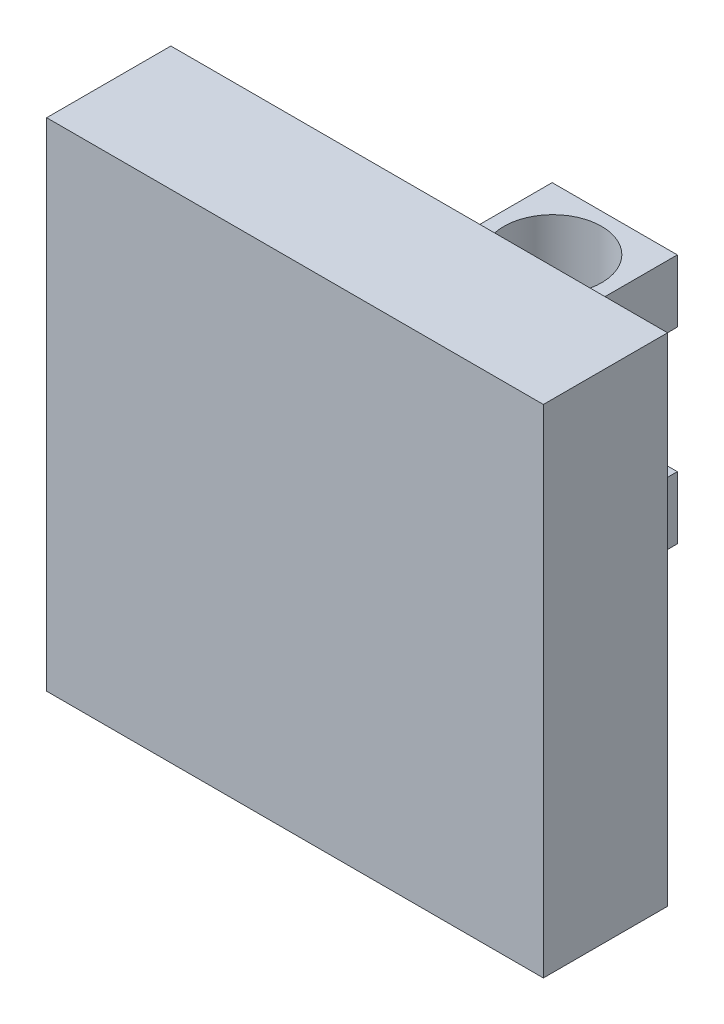
SolidWorks part; units mm, degrees
material "Acrylic (Medium-high impact)"
ref_plane "Front Plane" through (0, 0, 0) normal (0, 0, 1) x (1, 0, 0)
ref_plane "Top Plane" through (0, 0, 0) normal (0, 1, 0) x (1, 0, 0)
ref_plane "Right Plane" through (0, 0, 0) normal (1, 0, 0) x (0, 0, -1)
sketch "Sketch1" plane through (0, 0, 0) normal (0, 0, 1) x (1, 0, 0)
  line L1 (-12.7, -12.7) -> (12.7, -12.7)
  line L2 (-12.7, -12.7) -> (-12.7, 12.7)
  line L3 (-12.7, 12.7) -> (12.7, 12.7)
  line L4 (12.7, -12.7) -> (12.7, 12.7)
  line L5 (-12.7, -12.7) -> (12.7, 12.7) construction
  line L6 (-12.7, 12.7) -> (12.7, -12.7) construction
  point P0 (0, 0)
extrude "Boss-Extrude1" add sketch "Sketch1" along normal blind 6.35
sketch "Sketch2" plane through (0, 0, 0) normal (0, 0, -1) x (-1, 0, 0)
  line L0 (-3.2, 3.2) -> (-3.2, 6.4)
  line L1 (-3.2, 3.2) -> (3.2, 3.2)
  line L2 (-3.2, 3.2) -> (-3.2, -3.2) construction
  line L3 (-3.2, -3.2) -> (3.2, -3.2)
  line L4 (3.2, 3.2) -> (3.2, -3.2) construction
  line L5 (-3.2, 3.2) -> (3.2, -3.2) construction
  line L6 (-3.2, -3.2) -> (3.2, 3.2) construction
  line L7 (3.2, 3.2) -> (3.2, 6.4)
  line L8 (-3.2, -3.2) -> (-3.2, -6.4)
  line L9 (3.2, -3.2) -> (3.2, -6.4)
  line L10 (-3.2, 6.4) -> (3.2, 6.4)
  line L11 (3.2, -6.4) -> (-3.2, -6.4)
  point P0 (0, 0)
extrude "Boss-Extrude2" add sketch "Sketch2" along normal blind 10
sketch "Sketch3" plane through (0, 6.4, 0) normal (0, 1, 0) x (1, 0, 0)
  line L0 (0, 0) -> (0, 10) construction
  line L3 (-3.2, 0) -> (3.2, 0) construction
  line L4 (-3.2, 10) -> (3.2, 10) construction
  circle A0 centre (0, 6.8304) radius 2.4987
extrude "Cut-Extrude1" cut sketch "Sketch3" against normal through all
